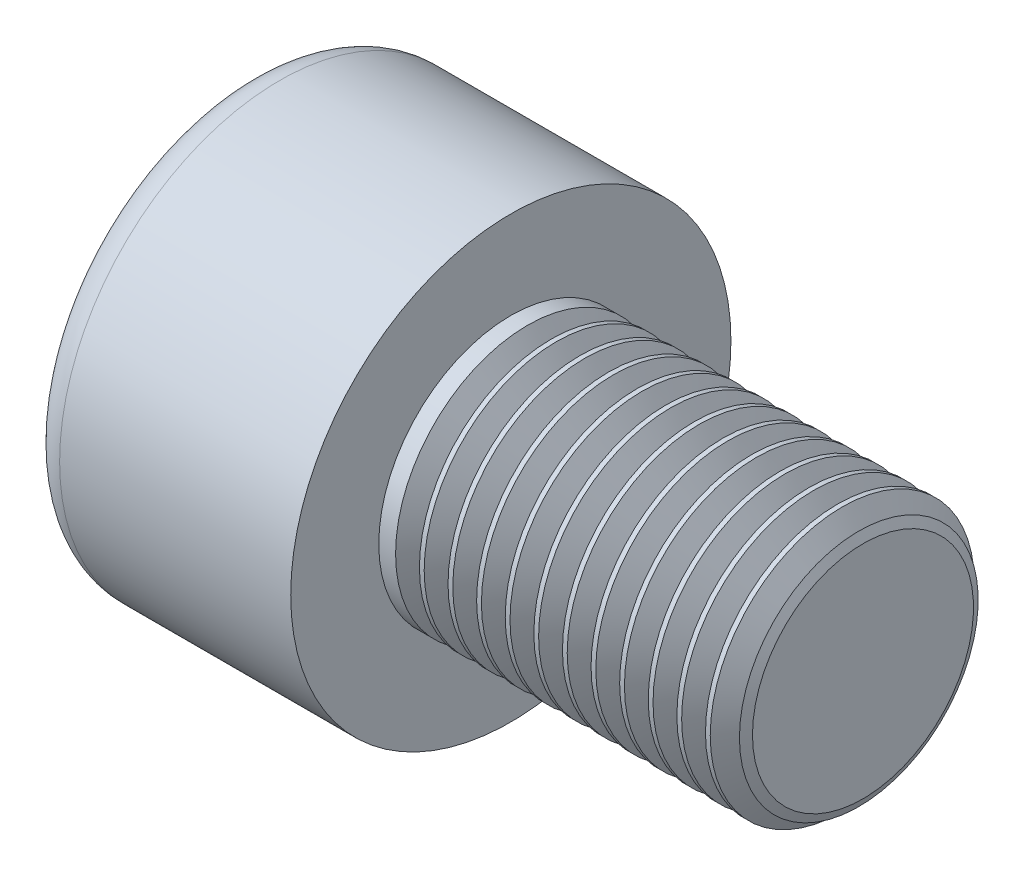
SolidWorks part; units mm, degrees
ref_plane "Front" through (0, 0, 0) normal (0, 0, 1) x (1, 0, 0)
ref_plane "Top" through (0, 0, 0) normal (0, 1, 0) x (1, 0, 0)
ref_plane "Right" through (0, 0, 0) normal (1, 0, 0) x (0, 0, -1)
sketch "Sketch1" plane through (0, 0, 0) normal (1, 0, 0) x (0, 0, -1)
  circle A0 centre (0, 0) radius 5
  dimension "dk" = 10
extrude "BaseHead" add sketch "Sketch1" along normal blind 6
sketch "Sketch2" plane through (6, 0, 0) normal (1, 0, 0) x (0, 0, -1)
  circle A0 centre (0, 0) radius 3
  dimension "d" = 6
extrude "BaseBody" add sketch "Sketch2" along normal blind 10
cosmetic thread "ThreadCosmetic1" [suppressed] parameters "b"=10, "D2"=4.917
sketch "Sketch3" plane through (0, 0, 0) normal (1, 0, 0) x (0, 0, -1)
  line L1 (2.8868, 0) -> (1.4434, 2.5)
  line L2 (1.4434, 2.5) -> (-1.4434, 2.5)
  line L3 (-1.4434, 2.5) -> (-2.8868, 0)
  line L4 (-2.8868, 0) -> (-1.4434, -2.5)
  line L5 (-1.4434, -2.5) -> (1.4434, -2.5)
  line L6 (1.4434, -2.5) -> (2.8868, 0)
  circle A0 centre (0, 0) radius 2.5 construction
  dimension "s" = 5
  dimension "e" = 5.7735
extrude "HexagonSocket" cut sketch "Sketch3" along normal blind 3
sketch "Sketch4" plane through (-4.1961, 0.75, 0) normal (0, 0, 1) x (-1, 0, 0)
  line L0 (-7.1961, 3.25) -> (-8.6395, 0.75)
  line L2 (-8.6395, 0.75) -> (-7.1961, 0.75)
  line L3 (-7.1961, 0.75) -> (-7.1961, 3.25)
  line L4 (-5.0351, 0.75) -> (0.839, 0.75) construction
  line L5 (-20.1961, 0.75) -> (-10.1961, 0.75) construction
  line L6 (-10.1961, 0.75) -> (-4.1961, 0.75) construction
  dimension "m" = 60
revolve "Cut-Revolve1" cut sketch "Sketch4" angle 360 about L4
fillet "HeadFillet" [suppressed] radius 0.25
fillet "TopFillet" radius 0.75 1 edges at (0, 0, -5)
chamfer "Chamfer1" distance 0.25 angle 45 1 edges at (16, 0, -3)
sketch "Sketch5" plane through (0, 0, 0) normal (0, 0, 1) x (1, 0, 0)
  line L0 (15.75, 2.531) -> (16.0207, 3)
  line L1 (16.0207, 3) -> (16.0207, 3.5415)
  line L2 (16.0207, 3.5415) -> (15.4793, 3.5415)
  line L3 (15.4793, 3.5415) -> (15.4793, 3)
  line L4 (15.4793, 3) -> (15.75, 2.531)
  line L5 (0, 0) -> (7.8886, 0) construction
  line L6 (15.75, -3) -> (15.75, 3) construction
  dimension "D1" = 6
  dimension "D2" = 0.5415
revolve "Cut-Revolve10" cut sketch "Sketch5" angle 360 about L5
pattern_linear "LPattern10" count 15 spacing 0.6498 along (-1, 0, 0) of "Cut-Revolve10"
sketch "草图1" plane through (16, 0, 0) normal (1, 0, 0) x (0, 0, -1)
  line L1 (-6.9447, 4.1281) -> (5.6331, 4.1281)
  line L2 (-6.9447, 4.1281) -> (-6.9447, -3.4616)
  line L3 (-6.9447, -3.4616) -> (5.6331, -3.4616)
  line L4 (5.6331, 4.1281) -> (5.6331, -3.4616)
extrude "切除-拉伸1" cut sketch "草图1" against normal blind 2
sketch "草图2" plane through (0, 0, 0) normal (0, 0, 1) x (1, 0, 0)
  line L0 (0, 0) -> (16.048, 0) construction
  line L1 (0, 4.25) -> (0, -4.25) construction
  line L2 (14, 2.5107) -> (13.71, 3.1246)
  line L3 (14, -2.8764) -> (14, 2.8764) construction
  line L4 (13.71, 3.1246) -> (14, 3.1246)
  line L5 (14, 3.1246) -> (14, 2.5107)
revolve "切除-旋转1" cut sketch "草图2" angle 360 about L0
equation "\"r1@TopFillet\" = \"d@Sketch2\" / 8"
equation "\"D1@Chamfer1\" = \"r@HeadFillet\""
equation "\"D1@Sketch5\" = \"d@Sketch2\""
equation "\"D2@Sketch5\" =  ( \"d@Sketch2\" - \"D2@ThreadCosmetic1\" )  / 2"
equation "\"D3@LPattern10\" = \"D2@Sketch5\" * 1.2"
equation "\"D1@LPattern10\" = \"b@ThreadCosmetic1\" / \"D3@LPattern10\""
